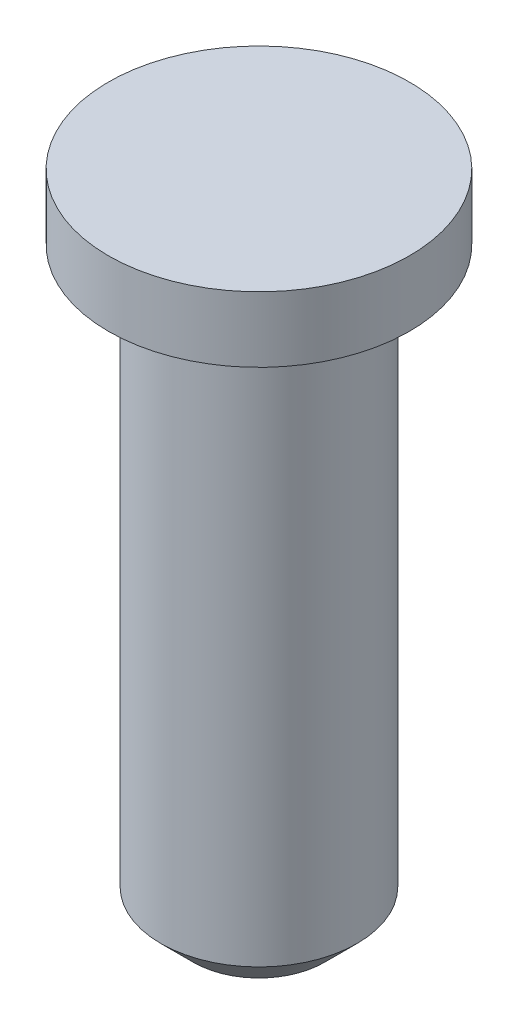
SolidWorks part; units mm, degrees
material "acero"
ref_plane "Alzado" through (0, 0, 0) normal (0, 0, 1) x (1, 0, 0)
ref_plane "Planta" through (0, 0, 0) normal (0, 1, 0) x (1, 0, 0)
ref_plane "Vista lateral" through (0, 0, 0) normal (1, 0, 0) x (0, 0, -1)
sketch "Croquis1" plane through (0, 0, 0) normal (0, 0, 1) x (1, 0, 0)
  line L0 (0, 0) -> (0, -60.9498) construction
  line L1 (0, 0) -> (2.3, 0)
  line L2 (2.3, 0) -> (2.3, -1)
  line L3 (2.3, -1) -> (1.5, -1)
  line L4 (1.5, -1) -> (1.5, -10)
  line L5 (1.5, -10) -> (0, -10)
  line L6 (0, -10) -> (0, 0)
  dimension "D1" = 10
  dimension "D2" = 1
  dimension "D3" = 4.6
  dimension "D4" = 3
revolve "Revolución1" add sketch "Croquis1" angle 360 about L0
chamfer "Chaflán1" distance 0.5 angle 45 1 edges at (0, -10, 1.5)
